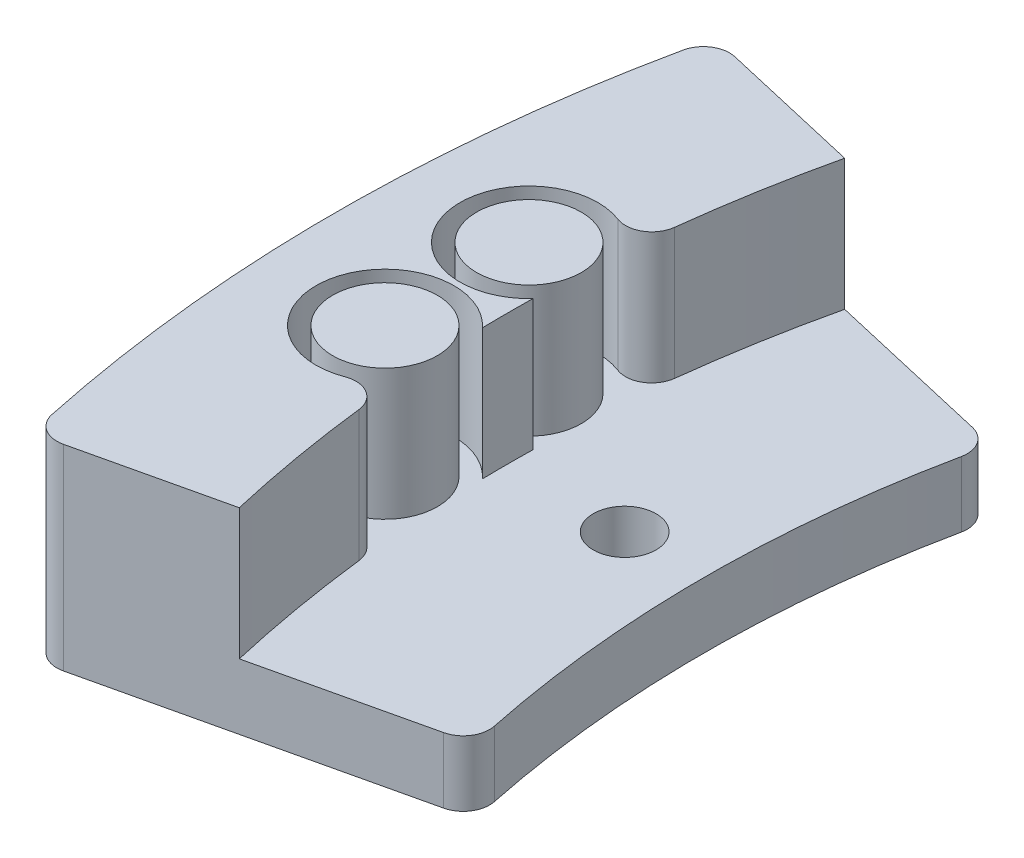
SolidWorks part; units mm, degrees
ref_plane "Front Plane" through (0, 0, 0) normal (0, 0, 1) x (1, 0, 0)
ref_plane "Top Plane" through (0, 0, 0) normal (0, 1, 0) x (1, 0, 0)
ref_plane "Right Plane" through (0, 0, 0) normal (1, 0, 0) x (0, 0, -1)
sketch "Sketch1" plane through (0, 0, 0) normal (0, 1, 0) x (1, 0, 0)
  line L0 (0, 0) -> (0, 25) construction
  line L1 (-0.7763, 12.5) -> (6.3973, 12.5) construction
  arc A0 (0, 25) -> (0, 0) centre (100.2522, 12.5) ccw
  circle A1 centre (6.3973, 12.5) radius 2.5
  dimension "D1" = 101.0285
  dimension "D3" = 5
  dimension "D2" = 25
  dimension "D4" = 7.1736
sketch "Sketch2" plane through (0, 0, 0) normal (0, 1, 0) x (1, 0, 0)
  line L0 (6.3973, 12.5) -> (100.2522, 12.5) construction
  line L1 (100.2522, 12.5) -> (-12.8025, 38.6007)
  line L2 (-12.8025, -13.6007) -> (100.2522, 12.5)
  line L3 (-0.7763, 12.5) -> (-15.7763, 12.5) construction
  circle A0 centre (6.3973, 12.5) radius 2.4
  arc A1 (-12.8025, 38.6007) -> (-12.8025, -13.6007) centre (100.2522, 12.5) ccw
  arc A2 (0, 25) -> (0, 0) centre (100.2522, 12.5) ccw construction
  dimension "D1" = 4.8
  dimension "D3" = 13
  dimension "D2" = 15
  dimension "D4" = 13
extrude "Boss-Extrude1" add sketch "Sketch2" along normal blind 5
sketch "Sketch3" plane through (0, 5, 0) normal (0, 1, 0) x (1, 0, 0)
  line L0 (100.2522, 12.5) -> (-12.8025, 38.6007) construction
  line L1 (-12.8025, -13.6007) -> (100.2522, 12.5) construction
  line L2 (0.0806, -10.6264) -> (-12.8025, -13.6007)
  line L3 (0.0806, 35.6264) -> (-12.8025, 38.6007)
  arc A0 (0, 25) -> (0, 0) centre (100.2522, 12.5) ccw construction
  arc A1 (1.8131, 35.2265) -> (1.8131, -10.2265) centre (100.2522, 12.5) ccw construction
  arc A2 (0.0806, 35.6264) -> (0.0806, -10.6264) centre (100.2522, 12.5) ccw
  arc A3 (-12.8025, 38.6007) -> (-12.8025, -13.6007) centre (100.2522, 12.5) ccw construction
  arc A4 (-12.8025, 38.6007) -> (-12.8025, -13.6007) centre (100.2522, 12.5) ccw
  dimension "D1" = 1.778
extrude "Boss-Extrude2" add sketch "Sketch3" along normal blind 10
sketch "Sketch4" plane through (0, 15, 0) normal (0, 1, 0) x (1, 0, 0)
  line L0 (-0.7763, 12.5) -> (6.3973, 12.5) construction
  circle A0 centre (-6.4126, 7) radius 4
  arc A1 (0.0806, 35.6264) -> (0.0806, -10.6264) centre (100.2522, 12.5) ccw construction
  circle A2 centre (-6.4126, 7) radius 5.27
  dimension "D2" = 8
  dimension "D3" = 1.27
  dimension "D1" = 5.5
extrude "Cut-Extrude1" cut sketch "Sketch4" against normal up to surface (10 mm away) up to face at (6.3973, 5, -10.1)
ref_plane "Plane1" through (0, 0, -12.5) normal (0, 0, 1) x (1, 0, 0)
mirror "Mirror1" about plane through (0, 0, -12.5) normal (0, 0, 1) of "Cut-Extrude1"
sketch "Sketch5" plane through (0, 5, 0) normal (0, 1, 0) x (1, 0, 0)
  line L0 (0.0806, -10.6264) -> (100.2522, 12.5) construction
  line L1 (100.2522, 12.5) -> (0.0806, 35.6264) construction
  line L2 (14.6962, -7.2522) -> (100.2522, 12.5)
  line L3 (100.2522, 12.5) -> (14.6962, 32.2522)
  arc A0 (14.6962, -7.2522) -> (14.6962, 32.2522) centre (100.2522, 12.5) cw
  dimension "D1" = 15
extrude "Cut-Extrude2" cut sketch "Sketch5" against normal through all
fillet "Fillet1" radius 2 6 edges at (-12.8025, 7.5, 13.6007) (-2.1895, 10, -3.8474) (-12.8025, 7.5, -38.6007) (-2.1895, 10, -21.1526) (14.6962, 2.5, -32.2522) (14.6962, 2.5, 7.2522)
